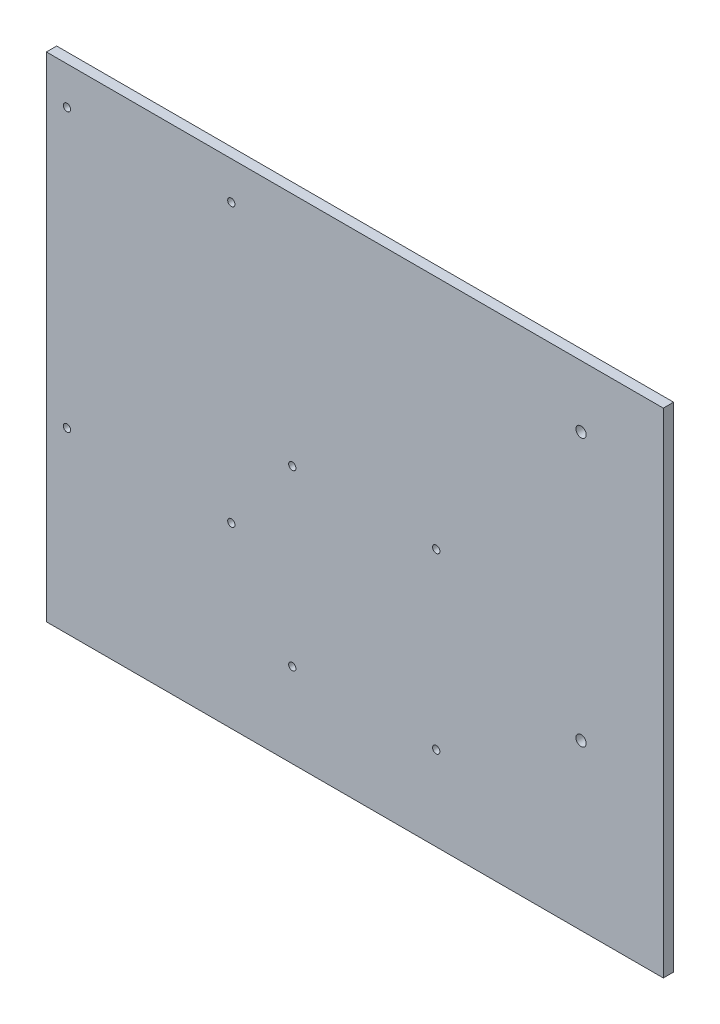
SolidWorks part; units mm, degrees
material "Acrylic (Medium-high impact)"
ref_plane "Front Plane" through (0, 0, 0) normal (0, 0, 1) x (1, 0, 0)
ref_plane "Top Plane" through (0, 0, 0) normal (0, 1, 0) x (1, 0, 0)
ref_plane "Right Plane" through (0, 0, 0) normal (1, 0, 0) x (0, 0, -1)
sketch "Sketch1" plane through (0, 0, 0) normal (0, 0, 1) x (1, 0, 0)
  line L1 (0, 0) -> (381, 0)
  line L2 (0, 0) -> (0, 304.8)
  line L3 (0, 304.8) -> (381, 304.8)
  line L4 (381, 0) -> (381, 304.8)
  dimension "D1" = 381
  dimension "D2" = 304.8
extrude "Boss-Extrude1" add sketch "Sketch1" along normal blind 6.35
hole_wizard "M4 Clearance Hole1" positions "Sketch4" profile "Sketch5" hole size "M4" standard "ANSI Metric" end condition through all
sketch "Sketch4" plane through (0, 0, 6.35) normal (0, 0, 1) x (1, 0, 0)
  line L6 (0, 304.8) -> (0, 0) construction
  line L7 (0, 0) -> (381, 0) construction
  point P0 (12.7, 110)
  point P2 (114.2, 110)
  point P15 (12.7, 281.5)
  point P17 (114.2, 281.5)
  dimension "D1" = 101.5
  dimension "D2" = 110
  dimension "D3" = 12.7
  dimension "D4" = 171.5
sketch "Sketch5" plane through (12.7, 110, 6.35) normal (1, 0, 0) x (0, -1, 0)
  line L0 (0, 0) -> (0, 6.35)
  line L1 (0, 6.35) -> (2.25, 6.35)
  line L2 (2.25, 6.35) -> (2.25, 0)
  line L5 (2.25, 0) -> (0, 0)
  line L11 (0, -6.35) -> (0, 107.95) construction
  dimension "Thru Hole Dia." = 4.5
  dimension "Thru Hole Depth" = 6.35
sketch "Sketch3" plane through (0, 0, 6.35) normal (0, 0, 1) x (1, 0, 0)
  line L0 (0, 0) -> (381, 0) construction
  line L3 (381, 0) -> (381, 304.8) construction
  line L4 (285.75, 293.3324) -> (374.65, 293.3324) construction
  line L5 (285.75, 293.3324) -> (285.75, 20.2824) construction
  line L6 (285.75, 20.2824) -> (374.65, 20.2824) construction
  line L7 (374.65, 293.3324) -> (374.65, 20.2824) construction
  line L8 (285.75, 293.3324) -> (374.65, 20.2824) construction
  line L9 (285.75, 20.2824) -> (374.65, 293.3324) construction
  circle A0 centre (330.2, 101.6) radius 3.175
  circle A1 centre (330.2, 266.7) radius 3.175
  point P12 (330.2, 156.8074)
  dimension "D2" = 6.35
  dimension "D3" = 6.35
  dimension "D1" = 165.1
  dimension "D4" = 101.6
  dimension "D5" = 88.9
  dimension "D6" = 273.05
extrude "Cut-Extrude2" cut sketch "Sketch3" against normal through all
extrude "Cut-Extrude5" cut sketch "Sketch8" against normal blind 6.35
sketch "Sketch8" plane through (190.518, -5.8963, 6.35) normal (0, 0, 1) x (1, 0, 0)
  circle A0 centre (-38.6719, 165.0958) radius 2.2542
  circle A1 centre (50.2281, 165.0958) radius 2.2542
  circle A2 centre (-38.6719, 57.9129) radius 2.2542
  circle A3 centre (50.2281, 57.9129) radius 2.2542
